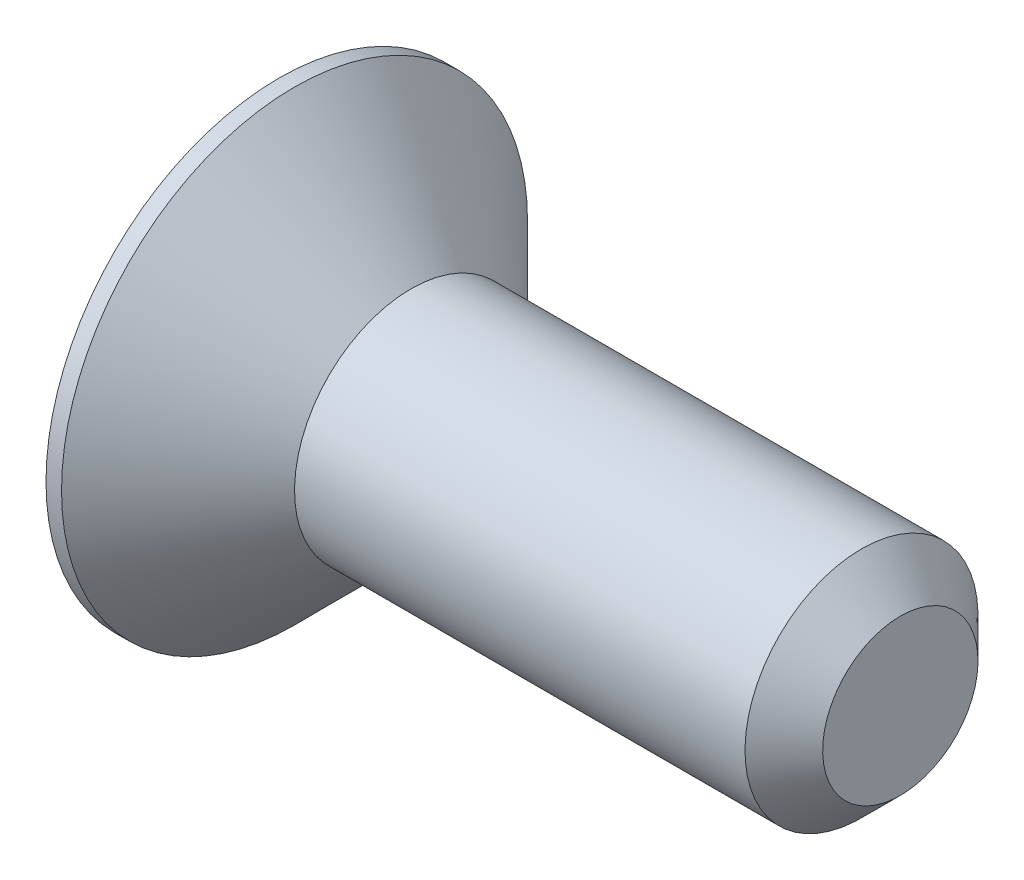
SolidWorks part; units mm, degrees
ref_plane "Plan de face" through (0, 0, 0) normal (0, 0, 1) x (1, 0, 0)
ref_plane "Plan de dessus" through (0, 0, 0) normal (0, 1, 0) x (1, 0, 0)
ref_plane "Plan de droite" through (0, 0, 0) normal (1, 0, 0) x (0, 0, -1)
sketch "Esquisse1" plane through (0, 0, 0) normal (0, 0, 1) x (1, 0, 0)
  line L0 (0, 0) -> (0, 3)
  line L1 (0, 3) -> (0.2, 3)
  line L2 (0.2, 3) -> (1.7, 1.5)
  line L3 (1.7, 1.5) -> (8, 1.5)
  line L4 (8, 1.5) -> (8, 0)
  line L5 (8, 0) -> (0, 0) construction
  line L6 (0, 0) -> (8, 0)
  dimension "D1" = 1.7
  dimension "D2" = 8
  dimension "D3" = 3
  dimension "D4" = 6
  dimension "D5" = 45
revolve "Révolution1" add sketch "Esquisse1" angle 360 about L5
chamfer "Chanfrein1" distance 0.5 angle 45 1 edges at (8, 1.5, 0)
sketch "Esquisse2" plane through (0, 0, 0) normal (-1, 0, 0) x (0, 0, 1)
  line L1 (0, 1.1547) -> (-1, 0.5774)
  line L2 (-1, 0.5774) -> (-1, -0.5774)
  line L3 (-1, -0.5774) -> (0, -1.1547)
  line L4 (0, -1.1547) -> (1, -0.5774)
  line L5 (1, -0.5774) -> (1, 0.5774)
  line L6 (1, 0.5774) -> (0, 1.1547)
  circle A0 centre (0, 0) radius 1 construction
  dimension "D1" = 2
extrude "Enlèv. mat.-Extru.1" cut sketch "Esquisse2" against normal blind 1.2
